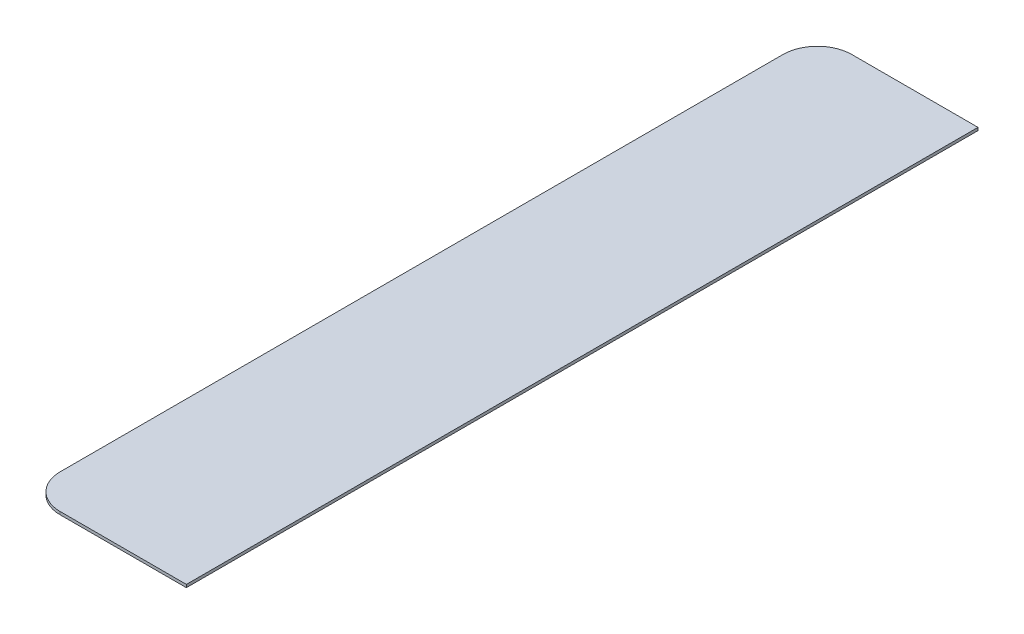
SolidWorks part; units mm, degrees
material "6061-T6 (SS)"
ref_plane "Front Plane" through (0, 0, 0) normal (0, 0, 1) x (1, 0, 0)
ref_plane "Top Plane" through (0, 0, 0) normal (0, 1, 0) x (1, 0, 0)
ref_plane "Right Plane" through (0, 0, 0) normal (1, 0, 0) x (0, 0, -1)
sketch "Sketch1" plane through (0, 0, 0) normal (0, 1, 0) x (1, 0, 0)
  line L1 (0, 0) -> (-279.4, 0)
  line L2 (0, 0) -> (0, -1752.6)
  line L3 (0, -1752.6) -> (-279.4, -1752.6)
  line L4 (-355.6, -76.2) -> (-355.6, -1676.4)
  arc A0 (-355.6, -1676.4) -> (-279.4, -1752.6) centre (-279.4, -1676.4) ccw
  arc A1 (-355.6, -76.2) -> (-279.4, 0) centre (-279.4, -76.2) cw
  dimension "D3" = 76.2
  dimension "D2" = 76.2
  dimension "D1" = 1752.6
  dimension "D4" = 355.6
extrude "Boss-Extrude1" add sketch "Sketch1" along normal blind 6.35
